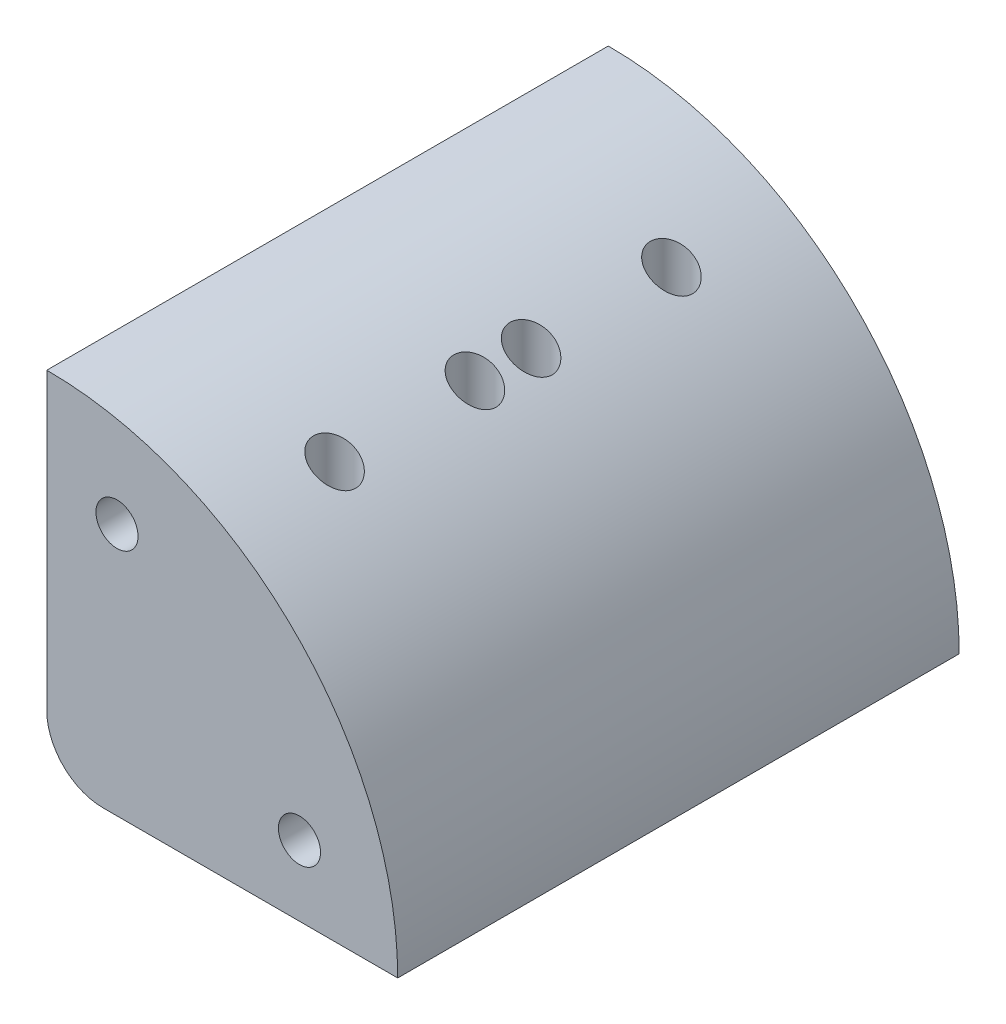
SolidWorks part; units mm, degrees
material "ABS"
ref_plane "Plano frontal" through (0, 0, 0) normal (0, 0, 1) x (1, 0, 0)
ref_plane "Plano superior" through (0, 0, 0) normal (0, 1, 0) x (1, 0, 0)
ref_plane "Plano direito" through (0, 0, 0) normal (1, 0, 0) x (0, 0, -1)
sketch "Esboço7" plane through (0, 0, 0) normal (0, 0, 1) x (1, 0, 0)
  line L0 (103.3573, -256.3355) -> (87.3573, -256.3355)
  line L1 (83.3573, -431.3355) -> (-66.6427, -431.3355) construction
  line L2 (108.3573, -406.3355) -> (108.3573, -256.3355) construction
  line L3 (83.3573, -231.3355) -> (-66.6427, -231.3355) construction
  line L4 (-91.6427, -406.3355) -> (-91.6427, -256.3355) construction
  line L5 (83.3573, -231.3355) -> (-66.6427, -231.3355) construction
  line L6 (83.3573, -231.3355) -> (83.3573, -236.3355)
  line L7 (83.3573, -236.3355) -> (-66.6427, -236.3355) construction
  line L8 (-66.6427, -231.3355) -> (-66.6427, -236.3355) construction
  line L9 (108.3573, -406.3355) -> (103.3573, -406.3355) construction
  line L10 (108.3573, -406.3355) -> (108.3573, -256.3355) construction
  line L11 (108.3573, -256.3355) -> (103.3573, -256.3355)
  line L12 (103.3573, -406.3355) -> (103.3573, -256.3355) construction
  line L13 (83.3573, -431.3355) -> (-66.6427, -431.3355) construction
  line L14 (83.3573, -431.3355) -> (83.3573, -426.3355) construction
  line L15 (83.3573, -426.3355) -> (-66.6427, -426.3355) construction
  line L16 (-66.6427, -431.3355) -> (-66.6427, -426.3355) construction
  line L17 (-91.6427, -406.3355) -> (-86.6427, -406.3355) construction
  line L18 (-91.6427, -406.3355) -> (-91.6427, -256.3355) construction
  line L19 (-91.6427, -256.3355) -> (-86.6427, -256.3355) construction
  line L20 (-86.6427, -406.3355) -> (-86.6427, -256.3355) construction
  line L21 (83.3573, -252.3355) -> (83.3573, -236.3355)
  arc A0 (-66.6427, -231.3355) -> (-91.6427, -256.3355) centre (-66.6427, -256.3355) ccw construction
  arc A1 (-66.6427, -431.3355) -> (-91.6427, -406.3355) centre (-66.6427, -406.3355) cw construction
  arc A2 (83.3573, -431.3355) -> (108.3573, -406.3355) centre (83.3573, -406.3355) ccw construction
  arc A3 (108.3573, -256.3355) -> (83.3573, -231.3355) centre (83.3573, -256.3355) ccw
  arc A4 (87.3573, -256.3355) -> (83.3573, -252.3355) centre (87.3573, -252.3355) cw
  point P6 (-91.6427, -231.3355)
  point P11 (108.3573, -431.3355)
  point P14 (108.3573, -231.3355)
  dimension "D3" = 25
  dimension "D9" = 4
  dimension "D1" = 200
  dimension "D2" = 200
  dimension "D4" = 5
  dimension "D5" = 5
  dimension "D6" = 5
  dimension "D7" = 5
  dimension "D8" = 150
extrude "Ressalto-extrusão3" add sketch "Esboço7" along normal blind 40
sketch "Esboço8" plane through (0, 0, 0) normal (0, 0, -1) x (-1, 0, 0)
  line L0 (-87.3573, -256.3355) -> (-108.3573, -256.3355) construction
  line L1 (-83.3573, -231.3355) -> (-83.3573, -252.3355) construction
  circle A0 centre (-88.3573, -238.3355) radius 1.5
  circle A1 centre (-101.3573, -251.3355) radius 1.5
  dimension "D1" = 3
  dimension "D2" = 5
  dimension "D3" = 7
  dimension "D4" = 3
  dimension "D5" = 7
  dimension "D6" = 5
extrude "Corte-extrusão1" cut sketch "Esboço8" against normal up to surface (40 mm away) up to face at (91.6946, -247.9982, 40)
sketch "Esboço9" plane through (0, -256.3355, 0) normal (0, -1, 0) x (1, 0, 0)
  line L1 (83.3573, 40) -> (83.3573, 0) construction
  line L4 (87.3573, 40) -> (108.3573, 40) construction
  line L5 (87.3573, 0) -> (108.3573, 0) construction
  circle A0 centre (95.8573, 8) radius 1.5
  circle A1 centre (95.8573, 18) radius 1.5
  circle A2 centre (95.8573, 22) radius 1.5
  circle A3 centre (95.8573, 32) radius 1.5
  dimension "D1" = 3
  dimension "D2" = 3
  dimension "D3" = 3
  dimension "D4" = 3
  dimension "D5" = 12.5
  dimension "D6" = 12.5
  dimension "D7" = 10
  dimension "D8" = 12.5
  dimension "D9" = 12.5
  dimension "D10" = 10
  dimension "D11" = 8
  dimension "D12" = 8
extrude "Corte-extrusão2" cut sketch "Esboço9" against normal through all
